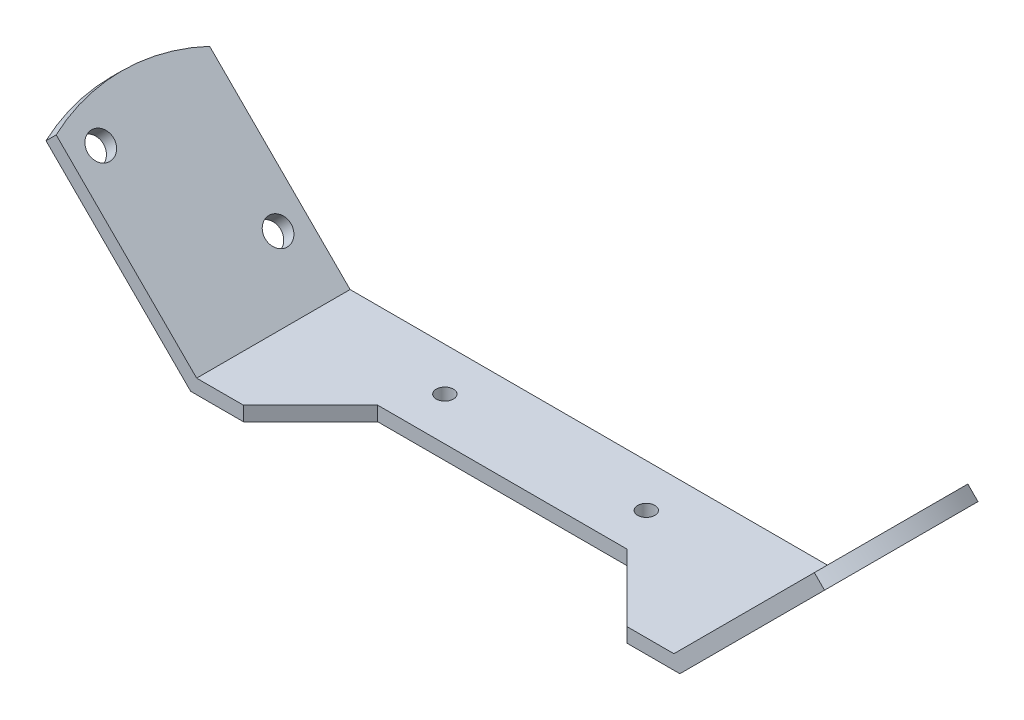
SolidWorks part; units mm, degrees
ref_plane "Front Plane" through (0, 0, 0) normal (0, 0, 1) x (1, 0, 0)
ref_plane "Top Plane" through (0, 0, 0) normal (0, 1, 0) x (1, 0, 0)
ref_plane "Right Plane" through (0, 0, 0) normal (1, 0, 0) x (0, 0, -1)
sketch "Middle Sketch" plane through (0, 0, 0) normal (0, 1, 0) x (1, 0, 0)
  line L0 (-13, -4.5) -> (-20, -11.5)
  line L1 (-13, -4.5) -> (13, -4.5)
  line L2 (-13, -4.5) -> (-13, 4.5)
  line L3 (-13, 4.5) -> (13, 4.5)
  line L4 (13, -4.5) -> (13, 4.5)
  line L5 (-13, -4.5) -> (13, 4.5) construction
  line L6 (-13, 4.5) -> (13, -4.5) construction
  line L7 (13, -4.5) -> (20, -11.5)
  line L8 (-20, 4.5) -> (-13, 4.5)
  line L13 (20, -11.5) -> (25.5, -11.5)
  line L14 (20, -11.5) -> (20, 4.5)
  line L15 (20, 4.5) -> (25.5, 4.5)
  line L16 (25.5, -11.5) -> (25.5, 4.5)
  line L17 (-20, -11.5) -> (-25.5, -11.5)
  line L18 (-20, -11.5) -> (-20, 4.5)
  line L19 (-20, 4.5) -> (-25.5, 4.5)
  line L20 (-25.5, -11.5) -> (-25.5, 4.5)
  line L21 (13, 4.5) -> (20, 4.5)
  point P0 (0, 0)
  dimension "D1" = 26
  dimension "D2" = 16
  dimension "D3" = 7
  dimension "D4" = 12.5
  dimension "D5" = 45
extrude "Middle Extrude" add sketch "Middle Sketch" along normal blind 1.5 contours L20 L17 L18 L19 | L18 L0 L2 L8 | L1 L4 L3 L2 | L21 L4 L7 L14 | L13 L16 L15 L14
ref_plane "Right Offset Plane" through (12.75, -12.75, 0) normal (0.7071, -0.7071, 0) x (0, 0, -1)
ref_plane "Left Offset Plane" through (-12.75, -12.75, 0) normal (-0.7071, -0.7071, 0) x (0, 0, -1)
sketch "Offshoot Right Plane Sketch" plane through (12.75, -12.75, 0) normal (0.7071, -0.7071, 0) x (0, 0, -1)
  line L1 (4.5, 18.0312) -> (-11.5, 18.0312)
  line L2 (4.5, 18.0312) -> (4.5, 39.3615)
  line L3 (4.5, 39.3615) -> (-11.5, 39.3615)
  line L4 (-11.5, 18.0312) -> (-11.5, 39.3615)
  arc A0 (4.5, 39.3615) -> (-11.5, 39.3615) centre (-3.5, 21.0312) ccw
  point P7 (-3.5, 41.0312)
  dimension "D1" = 20
  dimension "D2" = 23
sketch "Offshoot Left Plane Sketch" plane through (-12.75, -12.75, 0) normal (-0.7071, -0.7071, 0) x (0, 0, -1)
  line L1 (4.5, -18.0312) -> (-11.5, -18.0312)
  line L2 (4.5, -18.0312) -> (4.5, -39.3615)
  line L3 (4.5, -39.3615) -> (-11.5, -39.3615)
  line L4 (-11.5, -18.0312) -> (-11.5, -39.3615)
  arc A0 (4.5, -39.3615) -> (-11.5, -39.3615) centre (-3.5, -21.0312) cw
  point P8 (-3.5, -41.0312)
  dimension "D1" = 20
  dimension "D2" = 23
extrude "Right Offshoot Extrude" add sketch "Offshoot Right Plane Sketch" against normal blind 1.5 contours L3 A0 | L4 L1 L2 L3
extrude "Left Offshoot Extrude" add sketch "Offshoot Left Plane Sketch" against normal blind 1.5 contours L1 L4 L3 L2 | A0 L3
sketch "Hole Locations Middle" plane through (0, 0, 0) normal (0, 1, 0) x (1, 0, 0)
  line L0 (-13, 4.5) -> (13, 4.5) construction
  line L1 (-25.5, -11.5) -> (-25.5, 4.5) construction
  point P0 (-10.5, 0)
  point P1 (10.5, 0)
  dimension "D1" = 4.5
  dimension "D2" = 15
  dimension "D3" = 21
sketch "Right Offshoot Hole Locations" plane through (12.75, -12.75, 0) normal (0.7071, -0.7071, 0) x (0, 0, -1)
  arc A0 (4.5, 39.3615) -> (-11.5, 39.3615) centre (-3.5, 21.0312) ccw construction
  point P0 (1.5, 25.0312)
  point P1 (-8.5, 37.0312)
  point P5 (-3.5, 41.0312)
  dimension "D1" = 12
  dimension "D2" = 4
  dimension "D3" = 10
  dimension "D4" = 5
sketch "Left Offshoot Hole Locations" plane through (-12.75, -12.75, 0) normal (-0.7071, -0.7071, 0) x (0, 0, -1)
  arc A0 (-11.5, -39.3615) -> (4.5, -39.3615) centre (-3.5, -21.0312) ccw construction
  point P0 (-8.5, -37.0312)
  point P1 (1.5, -25.0312)
  point P5 (-3.5, -41.0312)
  dimension "D1" = 5
  dimension "D2" = 4
  dimension "D3" = 10
  dimension "D4" = 12
hole_wizard "Ø2.7 (2.7) Diameter Hole1" positions "Sketch7" profile "Sketch8" hole size "Ø2.7" standard "ANSI Metric" end condition through all
sketch "Sketch7" plane through (-11.6893, -11.6893, 0) normal (0.7071, 0.7071, 0) x (0.7071, -0.7071, 0)
  point P0 (-37.0312, -8.5)
  point P3 (-25.0312, 1.5)
sketch "Sketch8" plane through (-37.8744, 14.4957, 8.5) normal (0, 0, 1) x (-0.7071, 0.7071, 0)
  line L0 (0, 0) -> (0, 13)
  line L1 (0, 13) -> (1.35, 13)
  line L2 (1.35, 13) -> (1.35, 0)
  line L5 (1.35, 0) -> (0, 0)
  line L11 (0, -6.35) -> (0, 107.95) construction
  dimension "Thru Hole Dia." = 2.7
  dimension "Thru Hole Depth" = 13
hole_wizard "Ø2.7 (2.7) Diameter Hole2" positions "Sketch9" profile "Sketch10" hole size "Ø2.7" standard "ANSI Metric" end condition through all
sketch "Sketch9" plane through (11.6893, -11.6893, 0) normal (-0.7071, 0.7071, 0) x (0.7071, 0.7071, 0)
  point P0 (25.0312, 1.5)
  point P3 (37.0312, -8.5)
sketch "Sketch10" plane through (29.3891, 6.0104, -1.5) normal (0, 0, 1) x (-0.7071, -0.7071, 0)
  line L0 (0, 0) -> (0, 13)
  line L1 (0, 13) -> (1.35, 13)
  line L2 (1.35, 13) -> (1.35, 0)
  line L5 (1.35, 0) -> (0, 0)
  line L11 (0, -6.35) -> (0, 107.95) construction
  dimension "Thru Hole Dia." = 2.7
  dimension "Thru Hole Depth" = 13
hole_wizard "Ø1.8 (1.8) Diameter Hole1" positions "Sketch11" profile "Sketch12" hole size "Ø1.8" standard "ANSI Metric" end condition through all
sketch "Sketch11" plane through (0, 1.5, 0) normal (0, 1, 0) x (1, 0, 0)
  point P0 (-10.5, 0)
  point P3 (10.5, 0)
sketch "Sketch12" plane through (-10.5, 1.5, 0) normal (1, 0, 0) x (0, 0, 1)
  line L0 (0, 0) -> (0, 1.5)
  line L1 (0, 1.5) -> (0.9, 1.5)
  line L2 (0.9, 1.5) -> (0.9, 0)
  line L5 (0.9, 0) -> (0, 0)
  line L11 (0, -6.35) -> (0, 107.95) construction
  dimension "Thru Hole Dia." = 1.8
  dimension "Thru Hole Depth" = 1.5
